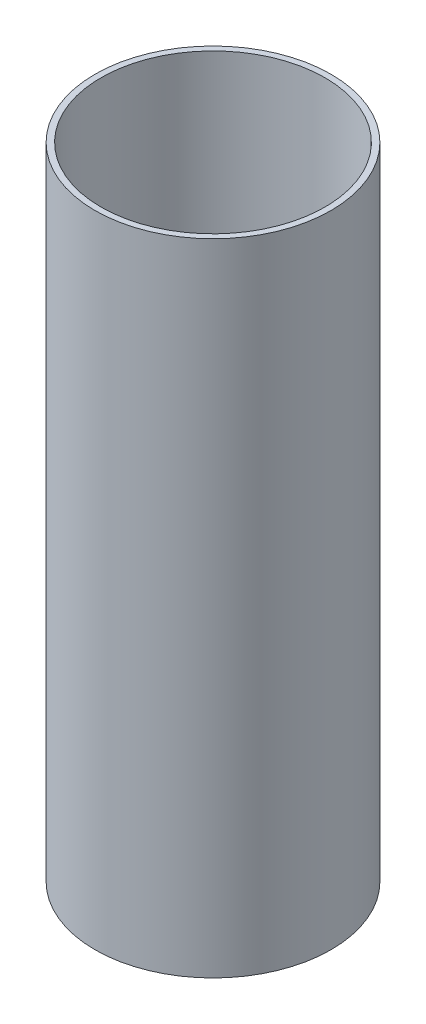
SolidWorks part; units mm, degrees
material "PVC Rigid"
ref_plane "Front Plane" through (0, 0, 0) normal (0, 0, 1) x (1, 0, 0)
ref_plane "Top Plane" through (0, 0, 0) normal (0, 1, 0) x (1, 0, 0)
ref_plane "Right Plane" through (0, 0, 0) normal (1, 0, 0) x (0, 0, -1)
sketch "Sketch1" plane through (0, 0, 0) normal (0, 1, 0) x (1, 0, 0)
  circle A0 centre (0, 0) radius 93.6625
  circle A1 centre (0, 0) radius 88.9
  dimension "D1" = 187.325
  dimension "D2" = 177.8
extrude "Boss-Extrude1" add sketch "Sketch1" along normal mid plane 508
